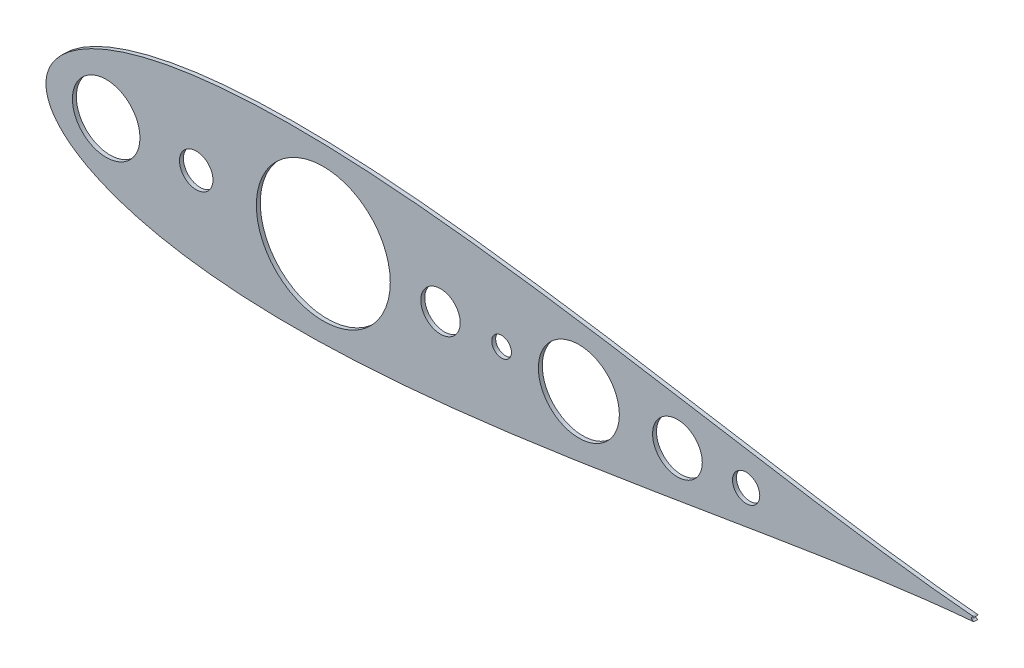
SolidWorks part; units mm, degrees
material "Balsa"
ref_plane "Front Plane" through (0, 0, 0) normal (0, 0, 1) x (1, 0, 0)
ref_plane "Top Plane" through (0, 0, 0) normal (0, 1, 0) x (1, 0, 0)
ref_plane "Right Plane" through (0, 0, 0) normal (1, 0, 0) x (0, 0, -1)
sketch "Sketch2" plane through (0, 0, 0) normal (0, 0, 1) x (1, 0, 0)
  circle A0 centre (0, 0) radius 10.795
  circle A1 centre (157.48, 0) radius 12.7
  circle A2 centre (196.85, 0) radius 6.35
  circle A3 centre (310.1922, 0) radius 16.0288
  circle A4 centre (354.4863, 0) radius 8.7799
  circle A5 centre (-58.0582, 0) radius 21.7634
  arc A6 (500.6849, -1.4713) -> (501.4171, -1.2039) centre (500.5625, 0) ccw
  arc A7 (501.4177, 1.2035) -> (500.6849, 1.4713) centre (500.5625, 0) ccw
  arc A8 (501.4177, 1.2035) -> (501.4171, -1.2039) centre (501.101, -0.0001) ccw
  circle A9 centre (246.6566, 0) radius 26.1032
  circle A10 centre (81.9194, 0) radius 43.167
  spline S0 degree 3 poles (500.6849, 1.4713) (500.2037, 1.5113) (496.577, 1.8168) (489.4347, 2.4769) (478.8329, 3.5798) (467.0785, 4.9331) (454.2156, 6.545) (440.3043, 8.4171) (425.4046, 10.5452) (409.5811, 12.9183) (392.901, 15.5196) (375.4341, 18.3258) (357.2527, 21.3079) (338.4311, 24.4315) (319.0453, 27.6573) (299.1732, 30.9414) (278.8943, 34.2363) (258.2895, 37.4913) (237.4414, 40.6536) (216.4338, 43.6686) (195.3523, 46.4813) (174.2836, 49.0368) (153.3164, 51.2813) (132.5404, 53.1631) (112.0472, 54.633) (91.9297, 55.6457) (72.2825, 56.1604) (53.2014, 56.1413) (34.7839, 55.5581) (17.1288, 54.388) (0.337, 52.6141) (-15.4891, 50.2283) (-30.2439, 47.2298) (-43.8181, 43.6287) (-56.0972, 39.446) (-66.9585, 34.7189) (-76.2701, 29.5103) (-83.893, 23.9256) (-89.6989, 18.1473) (-93.6295, 12.4809) (-95.8213, 7.3688) (-96.7064, 3.2678) (-96.908, 0) (-96.7064, -3.2678) (-95.8213, -7.3688) (-93.6295, -12.4809) (-89.6989, -18.1473) (-83.893, -23.9256) (-76.2701, -29.5103) (-66.9585, -34.7189) (-56.0972, -39.446) (-43.8181, -43.6287) (-30.2439, -47.2298) (-15.4891, -50.2283) (0.337, -52.6141) (17.1288, -54.388) (34.7839, -55.5581) (53.2014, -56.1413) (72.2825, -56.1604) (91.9297, -55.6457) (112.0472, -54.633) (132.5404, -53.1631) (153.3164, -51.2813) (174.2836, -49.0368) (195.3523, -46.4813) (216.4338, -43.6686) (237.4414, -40.6536) (258.2895, -37.4913) (278.8943, -34.2363) (299.1732, -30.9414) (319.0453, -27.6573) (338.4311, -24.4315) (357.2527, -21.3079) (375.4341, -18.3258) (392.901, -15.5196) (409.5811, -12.9183) (425.4046, -10.5452) (440.3043, -8.4171) (454.2156, -6.545) (467.0785, -4.9331) (478.8329, -3.5798) (489.4347, -2.4769) (496.577, -1.8168) (500.2037, -1.5113) (500.6849, -1.4713) knots 0.020157 0.020157 0.020157 0.020157 0.021271 0.028553 0.036781 0.04592 0.055932 0.066773 0.078397 0.090755 0.103793 0.117456 0.131686 0.146422 0.1616 0.177156 0.193024 0.209135 0.225421 0.241812 0.258238 0.274629 0.290914 0.307025 0.322893 0.338448 0.353626 0.368361 0.38259 0.396253 0.40929 0.421647 0.43327 0.444109 0.454119 0.463255 0.471479 0.478755 0.485052 0.490344 0.49461 0.497833 0.5 0.502167 0.50539 0.509656 0.514948 0.521245 0.528521 0.536745 0.545881 0.555891 0.56673 0.578353 0.59071 0.603747 0.61741 0.631639 0.646374 0.661552 0.677107 0.692975 0.709086 0.725371 0.741762 0.758188 0.774579 0.790865 0.806976 0.822844 0.8384 0.853578 0.868314 0.882544 0.896207 0.909245 0.921603 0.933227 0.944068 0.95408 0.963219 0.971447 0.978729 0.979843 0.979843 0.979843 0.979843
  dimension "D1" = 43.5268
  dimension "D2" = 21.59
extrude "Boss-Extrude1" add sketch "Sketch2" along normal blind 2.54
